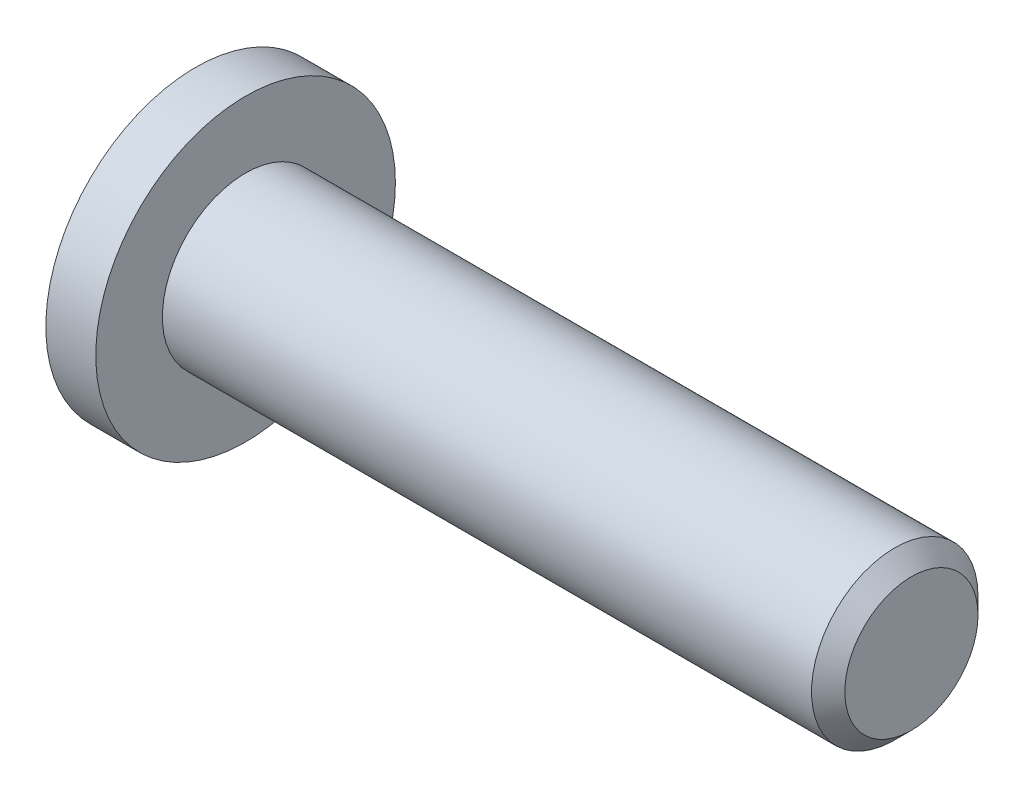
SolidWorks part; units mm, degrees
material "AISI 1035 Steel (SS)"
ref_plane "Front Plane" through (0, 0, 0) normal (0, 0, 1) x (1, 0, 0)
ref_plane "Top Plane" through (0, 0, 0) normal (0, 1, 0) x (1, 0, 0)
ref_plane "Right Plane" through (0, 0, 0) normal (1, 0, 0) x (0, 0, -1)
sketch "Sketch1" plane through (0, 0, 0) normal (1, 0, 0) x (0, 0, -1)
  circle A0 centre (0, 0) radius 4.5
  dimension "D1" = 9
extrude "Head" add sketch "Sketch1" along normal blind 1.5
sketch "Sketch2" plane through (1.5, 0, 0) normal (1, 0, 0) x (0, 0, -1)
  circle A0 centre (0, 0) radius 2.5
  dimension "D1" = 5
extrude "Body" add sketch "Sketch2" along normal blind 20
cosmetic thread "Cosmetic Thread2" parameters "D1"=28, "D2"=4.11
sketch "Sketch3" plane through (0, 0, 0) normal (-1, 0, 0) x (0, 0, 1)
  line L1 (0, 1.7321) -> (-1.5, 0.866)
  line L2 (-1.5, 0.866) -> (-1.5, -0.866)
  line L3 (-1.5, -0.866) -> (0, -1.7321)
  line L4 (0, -1.7321) -> (1.5, -0.866)
  line L5 (1.5, -0.866) -> (1.5, 0.866)
  line L6 (1.5, 0.866) -> (0, 1.7321)
  circle A0 centre (0, 0) radius 1.5 construction
  dimension "D1" = 3
extrude "Drive" cut sketch "Sketch3" against normal blind 3
chamfer "Chamfer1" distance 0.5 angle 45 1 edges at (21.5, 0, -2.5)
